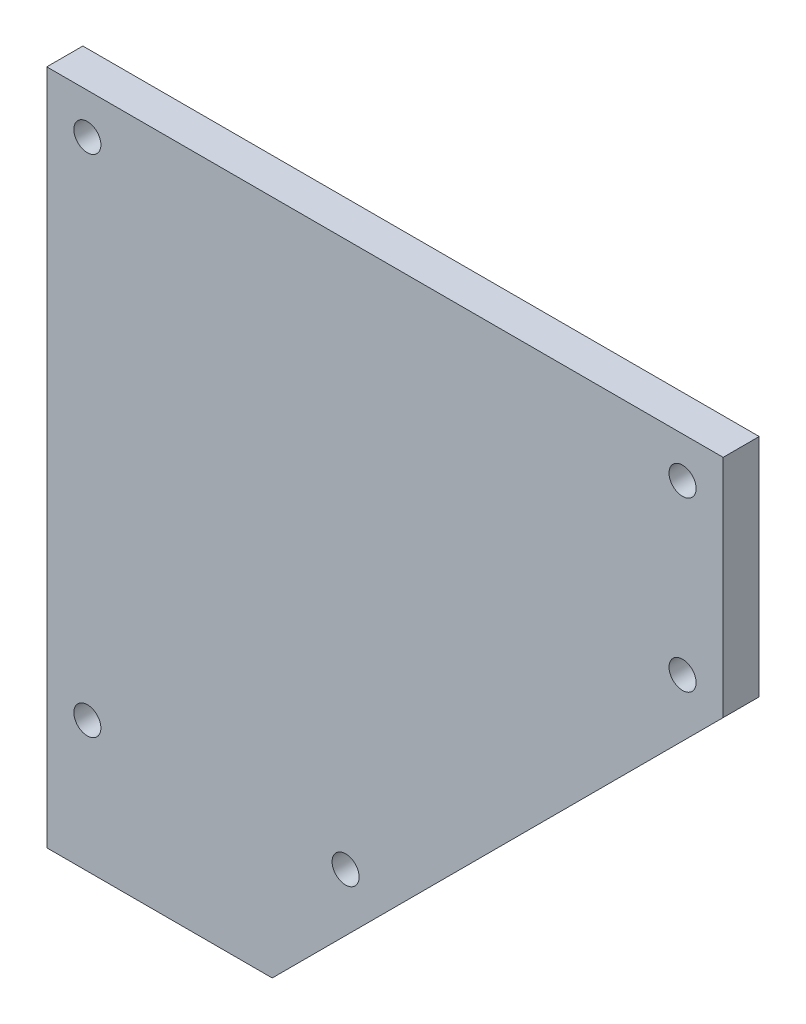
SolidWorks part; units mm, degrees
ref_plane "Front Plane" through (0, 0, 0) normal (0, 0, 1) x (1, 0, 0)
ref_plane "Top Plane" through (0, 0, 0) normal (0, 1, 0) x (1, 0, 0)
ref_plane "Right Plane" through (0, 0, 0) normal (1, 0, 0) x (0, 0, -1)
sketch "Sketch1" plane through (0, 0, 0) normal (0, 0, 1) x (1, 0, 0)
  line L0 (0, 0) -> (0, -65)
  line L1 (0, -65) -> (0, -75)
  line L2 (0, -75) -> (25, -75)
  line L3 (25, -75) -> (75, -25)
  line L4 (75, -25) -> (75, 0)
  line L5 (75, 0) -> (0, 0)
  line L6 (0, -65) -> (35, -65) construction
  line L7 (70.5, -4.5) -> (4.5, -4.5) construction
  line L8 (4.5, -4.5) -> (4.5, -65) construction
  line L9 (4.5, -65) -> (4.5, -70.5) construction
  line L10 (4.5, -70.5) -> (23.136, -70.5) construction
  line L11 (23.136, -70.5) -> (70.5, -23.136) construction
  line L12 (70.5, -23.136) -> (70.5, -4.5) construction
  line L13 (28.636, -65) -> (28.636, -60.5) construction
  line L14 (4.5, -4.5) -> (0, -4.5) construction
  line L15 (33.136, -60.5) -> (4.5, -60.5) construction
  circle A0 centre (4.5, -4.5) radius 1.5
  circle A1 centre (70.5, -4.5) radius 1.5
  circle A2 centre (70.5, -23.136) radius 1.5
  circle A3 centre (4.5, -60.5) radius 1.5
  circle A4 centre (33.136, -60.5) radius 1.5
  dimension "D6" = 3
  dimension "D1" = 65
  dimension "D2" = 10
  dimension "D3" = 25
  dimension "D4" = 135
  dimension "D5" = 4.5
extrude "Boss-Extrude1" add sketch "Sketch1" along normal blind 4
